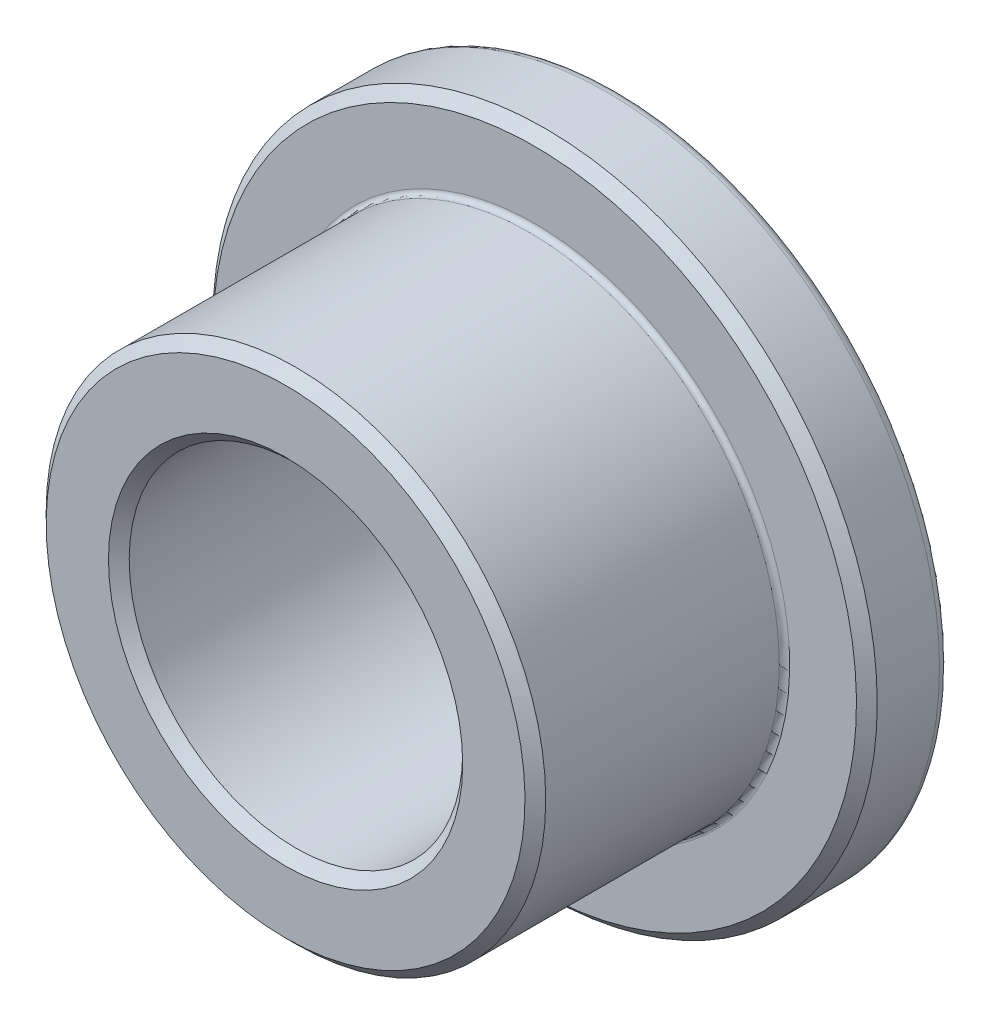
SolidWorks part; units mm, degrees
ref_plane "Front Plane" through (0, 0, 0) normal (0, 0, 1) x (1, 0, 0)
ref_plane "Top Plane" through (0, 0, 0) normal (0, 1, 0) x (1, 0, 0)
ref_plane "Right Plane" through (0, 0, 0) normal (1, 0, 0) x (0, 0, -1)
sketch "Sketch1" plane through (0, 0, 0) normal (0, 0, 1) x (1, 0, 0)
  circle A0 centre (0, 0) radius 3.1877
  circle A1 centre (0, 0) radius 4.7752
  circle A2 centre (0, 0) radius 6.35
  point P5 (0, 4.7752)
  point P6 (0, 3.1877)
  point P7 (0, 6.35)
  dimension "ID" = 6.3754
  dimension "OD" = 9.5504
  dimension "Flange OD" = 12.7
sketch "Sketch2" plane through (0, 0, 0) normal (1, 0, 0) x (0, 0, -1)
  line L0 (3.175, 0) -> (-3.175, 0)
  line L1 (3.175, 0) -> (3.175, 6.35)
  line L2 (3.175, 6.35) -> (1.5875, 6.35)
  line L3 (1.5875, 6.35) -> (1.5875, 4.7752)
  line L4 (1.5875, 4.7752) -> (-3.175, 4.7752)
  line L5 (-3.175, 4.7752) -> (-3.175, 3.1877)
  line L6 (-3.175, 3.1877) -> (3.175, 3.1877)
  point P4 (0, 0)
  dimension "Flange Thickness" = 1.5875
  dimension "Length" = 6.35
sketch "Sketch3" plane through (0, 0, 0) normal (1, 0, 0) x (0, 0, -1)
  line L0 (3.175, 6.35) -> (1.5875, 6.35) construction
  line L1 (1.5875, 6.35) -> (1.5875, 4.7752) construction
  line L2 (1.5875, 4.7752) -> (-3.175, 4.7752) construction
  line L3 (-3.175, 3.1877) -> (3.175, 3.1877) construction
  line L4 (-3.175, 4.7752) -> (-3.175, 3.1877) construction
  line L5 (3.175, 6.35) -> (1.5875, 6.35)
  line L6 (1.5875, 6.35) -> (1.5875, 4.7752)
  line L7 (1.5875, 4.7752) -> (-3.175, 4.7752)
  line L8 (-3.175, 3.1877) -> (3.175, 3.1877)
  line L9 (-3.175, 4.7752) -> (-3.175, 3.1877)
  line L10 (3.175, 6.35) -> (3.175, 3.1877)
revolve "Revolve1" add sketch "Sketch3" angle 360 about L0
chamfer "Chamfer1" distance 0.1984 angle 45 3 edges at (0, 6.35, -1.5875) (0, 4.7752, 3.175) (0, 3.1877, 3.175)
fillet "Fillet1" radius 0.1984 1 edges at (0, 6.35, -3.175)
fillet "Fillet2" radius 0.0992 1 edges at (0, 4.7752, -1.5875)
equation "\"D1@Chamfer1\"=\"Flange Thickness@Sketch2\"*.125"
equation "\"D1@Fillet1\"=\"D1@Chamfer1\""
equation "\"D1@Fillet2\"=\"D1@Fillet1\"*.5"
